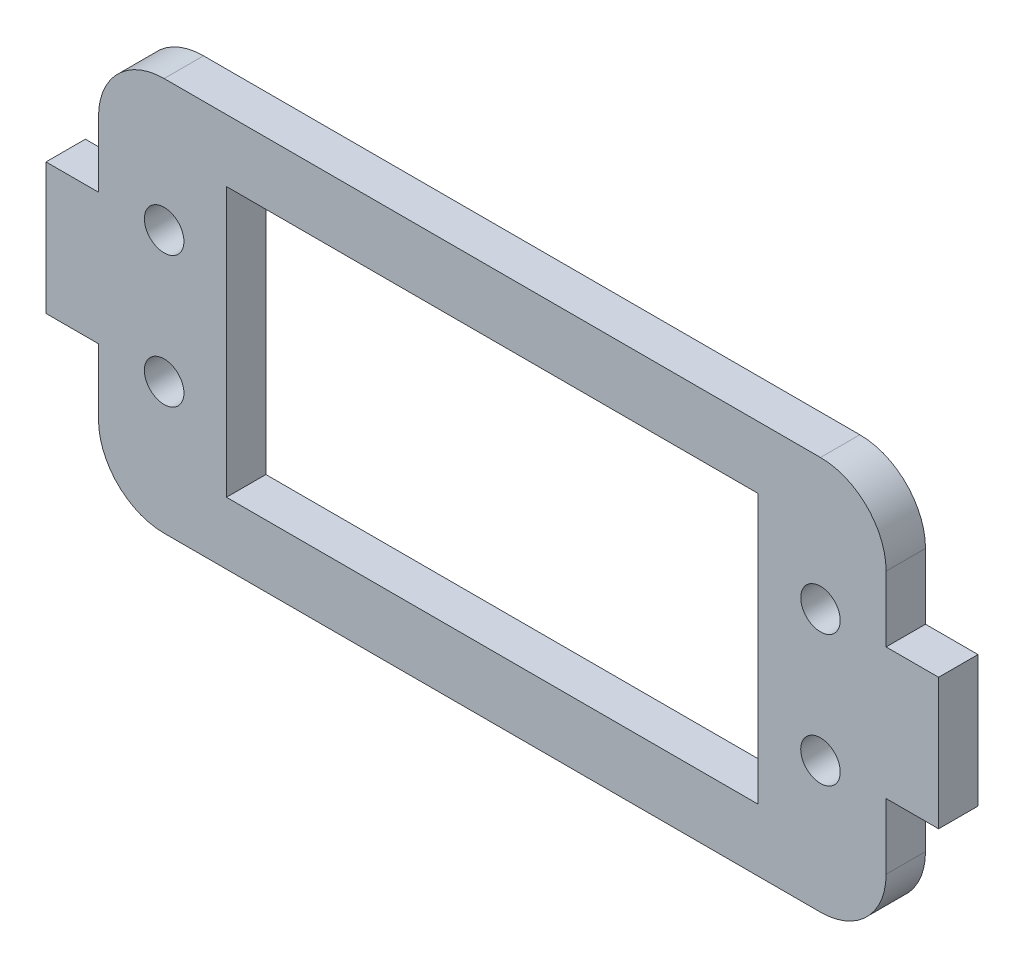
SolidWorks part; units mm, degrees
material "Balsa"
ref_plane "Alzado" through (0, 0, 0) normal (0, 0, 1) x (1, 0, 0)
ref_plane "Planta" through (0, 0, 0) normal (0, 1, 0) x (1, 0, 0)
ref_plane "Vista lateral" through (0, 0, 0) normal (1, 0, 0) x (0, 0, -1)
sketch "Croquis1" plane through (0, 0, 0) normal (0, 0, 1) x (1, 0, 0)
  line L0 (-30, -5) -> (-30, -15)
  line L1 (-30, 15) -> (30, 15)
  line L2 (-30, 15) -> (-30, 5)
  line L3 (-30, -15) -> (30, -15)
  line L4 (30, 15) -> (30, 5)
  line L5 (-30, 15) -> (30, -15) construction
  line L6 (-30, -15) -> (30, 15) construction
  line L7 (30, -5) -> (34, -5)
  line L9 (30, 5) -> (34, 5)
  line L10 (34, -5) -> (34, 5)
  line L13 (-30, -5) -> (-34, -5)
  line L15 (-30, 5) -> (-34, 5)
  line L16 (-34, -5) -> (-34, 5)
  line L17 (30, -5) -> (30, -15)
  point P0 (0, 0)
  point P6 (30, 0)
  point P11 (-30, 0)
  dimension "D1" = 60
  dimension "D2" = 30
  dimension "D3" = 10
  dimension "D4" = 10
extrude "Saliente-Extruir1" add sketch "Croquis1" along normal blind 3
sketch "Croquis2" plane through (0, 0, 3) normal (0, 0, 1) x (1, 0, 0)
  line L0 (0, 0) -> (0, 3.9387) construction
  line L1 (-20.25, 10.25) -> (20.25, 10.25)
  line L2 (-20.25, 10.25) -> (-20.25, -10.25)
  line L3 (-20.25, -10.25) -> (20.25, -10.25)
  line L4 (20.25, 10.25) -> (20.25, -10.25)
  line L5 (-20.25, 10.25) -> (20.25, -10.25) construction
  line L6 (-20.25, -10.25) -> (20.25, 10.25) construction
  line L7 (0, 3.9387) -> (0, 0) construction
  line L8 (0, 0) -> (3.4464, 0) construction
  circle A0 centre (25, 5) radius 1.5052
  circle A1 centre (-25, 5) radius 1.5052
  circle A2 centre (25, -5) radius 1.5052
  circle A3 centre (-25, -5) radius 1.5052
  point P0 (0, 0)
  dimension "D1" = 40.5
  dimension "D2" = 20.5
  dimension "D3" = 25
  dimension "D4" = 5
extrude "Cortar-Extruir1" cut sketch "Croquis2" against normal up to next
fillet "Redondeo1" radius 5 4 edges at (30, -15, 1.5) (-30, -15, 1.5) (30, 15, 1.5) (-30, 15, 1.5)
